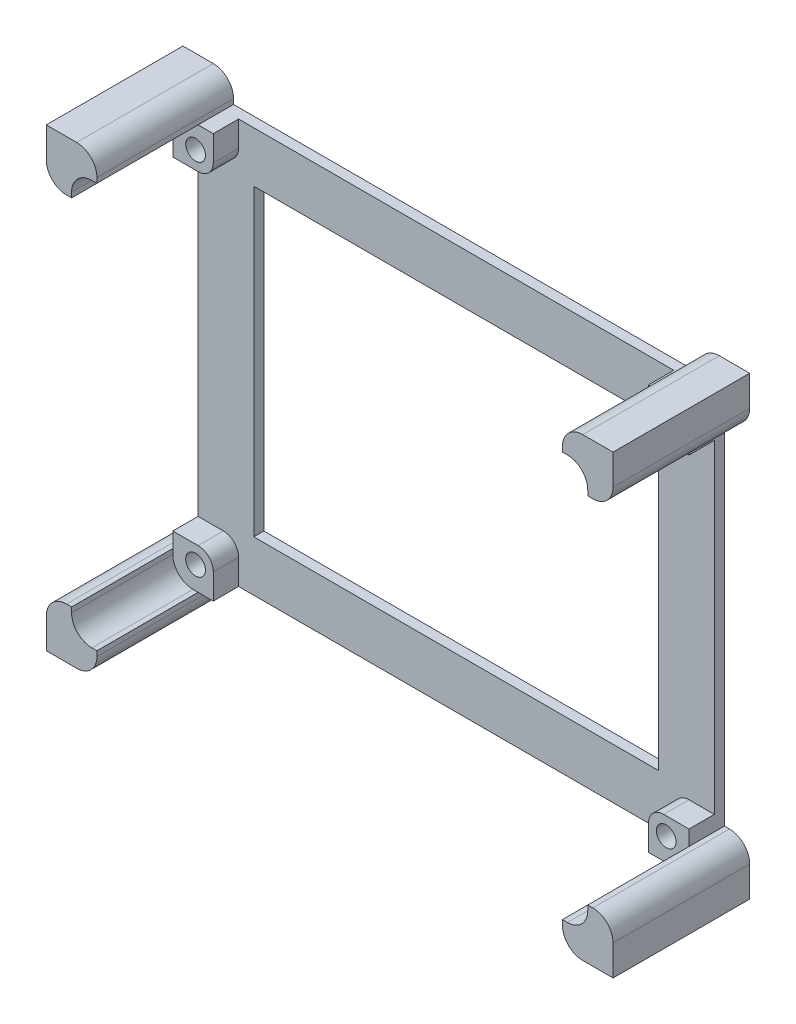
SolidWorks part; units mm, degrees
ref_plane "Front Plane" through (0, 0, 0) normal (0, 0, 1) x (1, 0, 0)
ref_plane "Top Plane" through (0, 0, 0) normal (0, 1, 0) x (1, 0, 0)
ref_plane "Right Plane" through (0, 0, 0) normal (1, 0, 0) x (0, 0, -1)
sketch "Sketch1" plane through (0, 0, 0) normal (0, 0, 1) x (1, 0, 0)
  line L0 (0, 75) -> (-5, 75)
  line L1 (5, 0) -> (97, 0)
  line L2 (0, 5) -> (0, 75)
  line L3 (5, 80) -> (97, 80)
  line L4 (102, 5) -> (102, 75)
  line L5 (-5, 75) -> (-5, 85)
  line L6 (-5, 85) -> (5, 85)
  line L7 (5, 85) -> (5, 80)
  line L8 (97, 0) -> (97, -5)
  line L9 (97, -5) -> (107, -5)
  line L10 (107, -5) -> (107, 5)
  line L11 (107, 5) -> (102, 5)
  line L12 (102, 75) -> (107, 75)
  line L13 (107, 75) -> (107, 85)
  line L14 (107, 85) -> (97, 85)
  line L15 (97, 85) -> (97, 80)
  line L16 (5, 0) -> (5, -5)
  line L17 (5, -5) -> (-5, -5)
  line L18 (-5, -5) -> (-5, 5)
  line L19 (-5, 5) -> (0, 5)
  dimension "D3" = 5
  dimension "D4" = 5
  dimension "D5" = 10
  dimension "D6" = 10
  dimension "D7" = 10
  dimension "D8" = 5
  dimension "D9" = 5
  dimension "D10" = 5
  dimension "D11" = 5
  dimension "D12" = 10
  dimension "D13" = 10
  dimension "D14" = 5
  dimension "D15" = 5
  dimension "D16" = 10
  dimension "D17" = 10
extrude "Boss-Extrude2" add sketch "Sketch1" along normal blind 27
sketch "Sketch3" plane through (0, 0, 27) normal (0, 0, 1) x (1, 0, 0)
  line L0 (-5, 85) -> (-5, 75) construction
  line L1 (0, 80) -> (102, 80)
  line L2 (0, 80) -> (0, 0)
  line L3 (0, 0) -> (102, 0)
  line L4 (102, 80) -> (102, 0)
  line L5 (5, 85) -> (-5, 85) construction
  point P4 (0, 0)
  dimension "D1" = 80
  dimension "D2" = 102
  dimension "D3" = 5
  dimension "D4" = 5
extrude "Cut-Extrude2" cut sketch "Sketch3" against normal blind 25
sketch "Sketch4" plane through (0, 0, 2) normal (0, 0, 1) x (1, 0, 0)
  line L1 (0, 80) -> (8, 80)
  line L2 (0, 80) -> (0, 72)
  line L3 (0, 72) -> (8, 72)
  line L4 (8, 80) -> (8, 72)
  line L5 (102, 80) -> (94, 80)
  line L6 (102, 80) -> (102, 72)
  line L7 (102, 72) -> (94, 72)
  line L8 (94, 80) -> (94, 72)
  line L9 (102, 0) -> (94, 0)
  line L10 (102, 0) -> (102, 8)
  line L11 (102, 8) -> (94, 8)
  line L12 (94, 0) -> (94, 8)
  line L13 (0, 0) -> (8, 0)
  line L14 (0, 0) -> (0, 8)
  line L15 (0, 8) -> (8, 8)
  line L16 (8, 0) -> (8, 8)
  dimension "D1" = 8
  dimension "D2" = 8
  dimension "D3" = 8
  dimension "D4" = 8
  dimension "D5" = 8
  dimension "D6" = 8
  dimension "D7" = 8
  dimension "D8" = 8
extrude "Boss-Extrude3" add sketch "Sketch4" along normal blind 5
sketch "Sketch7" plane through (0, 0, 7) normal (0, 0, 1) x (1, 0, 0)
  line L0 (4.5, 75.5) -> (97.5, 75.5) construction
  line L1 (97.5, 75.5) -> (97.5, 4.5) construction
  line L2 (94, 80) -> (8, 80) construction
  line L3 (102, 8) -> (102, 72) construction
  circle A0 centre (4.5, 75.5) radius 1.95
  circle A1 centre (97.5, 75.5) radius 1.95
  circle A2 centre (97.5, 4.5) radius 1.95
  circle A3 centre (4.5, 4.5) radius 1.95
  point P8 (51, 75.5)
  point P11 (51, 80)
  point P12 (97.5, 40)
  point P15 (102, 40)
  point P16 (0, 0)
  point P17 (0, 0)
  dimension "D1" = 3.9
  dimension "D2" = 93
  dimension "D3" = 71
extrude "Cut-Extrude3" cut sketch "Sketch7" against normal blind 3
fillet "Fillet2" radius 3 4 edges at (94, 8, 4.5) (94, 72, 4.5) (8, 8, 4.5) (8, 72, 4.5)
fillet "Fillet3" radius 4 12 edges at (97, 85, 13.5) (107, 75, 13.5) (-5, 75, 13.5) (5, 85, 13.5) (5, -5, 13.5) (-5, 5, 13.5) (107, 5, 13.5) (97, -5, 13.5) (0, 0, 17) (102, 0, 17) (102, 80, 17) (0, 80, 17)
sketch "Sketch8" plane through (0, 0, 2) normal (0, 0, 1) x (1, 0, 0)
  line L1 (11, 70) -> (91, 70)
  line L2 (11, 70) -> (11, 10)
  line L3 (11, 10) -> (91, 10)
  line L4 (91, 70) -> (91, 10)
  line L7 (0, 72) -> (0, 8) construction
  line L8 (94, 80) -> (8, 80) construction
  point P4 (11, 40)
  point P7 (0, 40)
  point P8 (51, 70)
  point P11 (51, 80)
  dimension "D1" = 80
  dimension "D2" = 60
extrude "Cut-Extrude4" cut sketch "Sketch8" against normal through all
